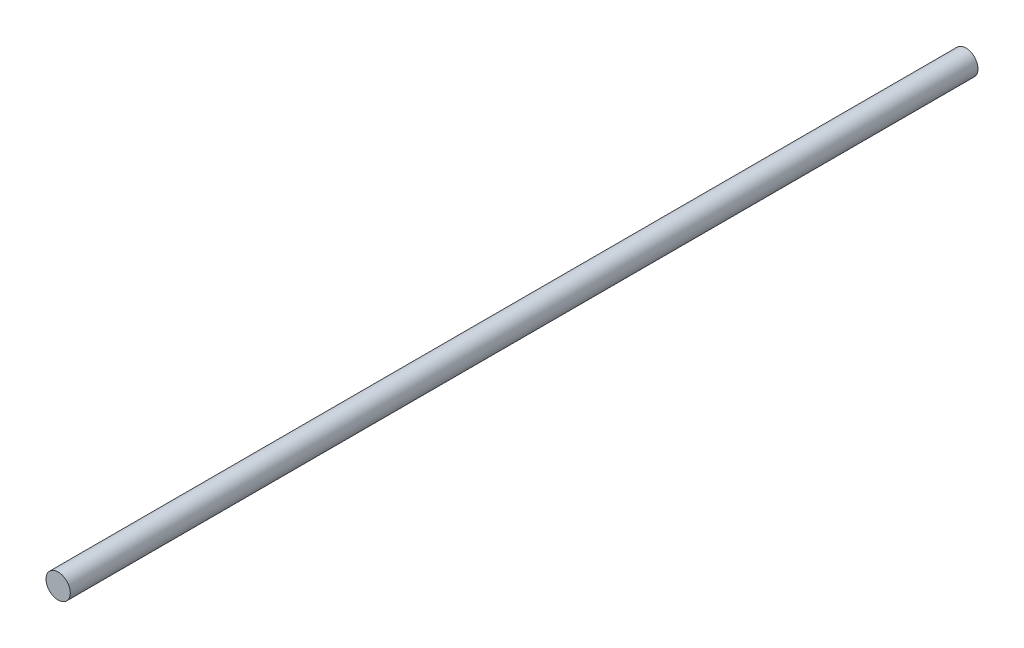
SolidWorks part; units mm, degrees
ref_plane "Front Plane" through (0, 0, 0) normal (0, 0, 1) x (1, 0, 0)
ref_plane "Top Plane" through (0, 0, 0) normal (0, 1, 0) x (1, 0, 0)
ref_plane "Right Plane" through (0, 0, 0) normal (1, 0, 0) x (0, 0, -1)
sketch "Sketch1" plane through (0, 0, 0) normal (0, 0, 1) x (1, 0, 0)
  circle A0 centre (0, 0) radius 1.5
extrude "Boss-Extrude1" add sketch "Sketch1" along normal blind 112
